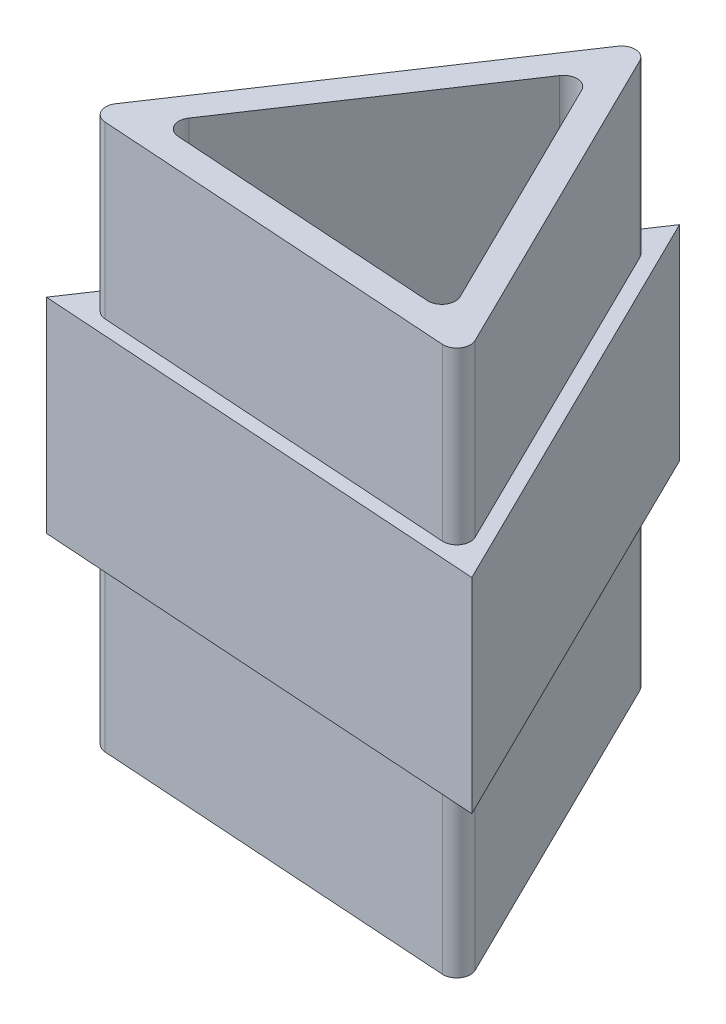
SolidWorks part; units mm, degrees
ref_plane "Front Plane" through (0, 0, 0) normal (0, 0, 1) x (1, 0, 0)
ref_plane "Top Plane" through (0, 0, 0) normal (0, 1, 0) x (1, 0, 0)
ref_plane "Right Plane" through (0, 0, 0) normal (1, 0, 0) x (0, 0, -1)
sketch "Sketch1" plane through (0, 0, 0) normal (0, 1, 0) x (1, 0, 0)
  line L0 (-0.2633, 13.2916) -> (-13.0895, -5.8864)
  line L1 (0, 17.2829) -> (-16.6778, -7.654)
  line L2 (-16.6778, -7.654) -> (13.2572, -9.6289)
  line L3 (13.2572, -9.6289) -> (0, 17.2829)
  line L4 (-13.0895, -5.8864) -> (9.9322, -7.4052)
  line L5 (9.9322, -7.4052) -> (-0.2633, 13.2916)
  circle A0 centre (-1.1402, 0) radius 8.6603 construction
  dimension "D1" = 30
  dimension "D2" = 2
extrude "Boss-Extrude1" add sketch "Sketch1" along normal blind 40
fillet "Fillet1" radius 1 6 edges at (9.9322, 20, 7.4052) (-0.2633, 20, -13.2916) (-13.0895, 20, 5.8864) (-16.6778, 20, 7.654) (13.2572, 20, 9.6289) (0, 20, -17.2829)
ref_plane "Plane1" through (0, 20, 0) normal (0, -1, 0) x (-1, 0, 0)
sketch "Sketch2" plane through (0, 20, 0) normal (0, -1, 0) x (-1, 0, 0)
  line L0 (-12.4918, -8.0752) -> (-0.7654, 15.7292)
  line L1 (-12.4918, -8.0752) -> (-0.7654, 15.7292)
  line L2 (14.9495, -7.7681) -> (-11.5289, -9.5149)
  line L3 (14.9495, -7.7681) -> (-11.5289, -9.5149)
  line L4 (0.9629, 15.8432) -> (15.7149, -6.2143)
  line L5 (0.9629, 15.8432) -> (15.7149, -6.2143)
  line L6 (18.4719, -8.5378) -> (-14.9196, -10.7408)
  line L7 (-14.9196, -10.7408) -> (-0.1317, 19.2786)
  line L9 (18.4719, -8.5378) -> (-0.1317, 19.2786)
  arc A0 (-12.4918, -8.0752) -> (-11.5289, -9.5149) centre (-11.5947, -8.5171) ccw
  arc A1 (-12.4918, -8.0752) -> (-11.5289, -9.5149) centre (-11.5947, -8.5171) ccw
  arc A2 (14.9495, -7.7681) -> (15.7149, -6.2143) centre (14.8836, -6.7702) ccw
  arc A3 (14.9495, -7.7681) -> (15.7149, -6.2143) centre (14.8836, -6.7702) ccw
  arc A4 (0.9629, 15.8432) -> (-0.7654, 15.7292) centre (0.1317, 15.2873) ccw
  arc A5 (0.9629, 15.8432) -> (-0.7654, 15.7292) centre (0.1317, 15.2873) ccw
  dimension "D1" = 1
  dimension "D2" = 1
  dimension "D3" = 1
extrude "Boss-Extrude2" add sketch "Sketch2" along normal mid plane 15
